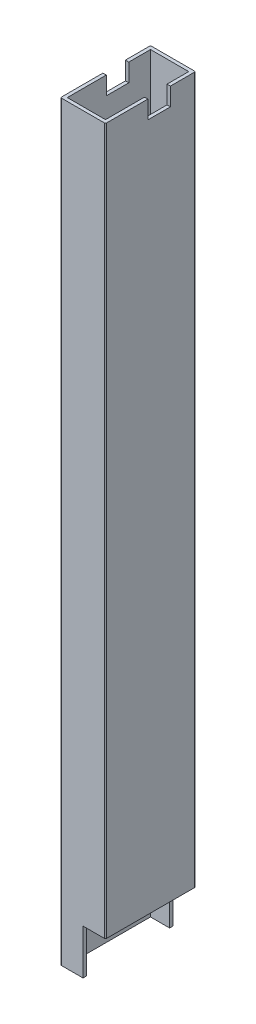
SolidWorks part; units mm, degrees
ref_plane "Front Plane" through (0, 0, 0) normal (0, 0, 1) x (1, 0, 0)
ref_plane "Top Plane" through (0, 0, 0) normal (0, 1, 0) x (1, 0, 0)
ref_plane "Right Plane" through (0, 0, 0) normal (1, 0, 0) x (0, 0, -1)
sketch "Sketch1" plane through (0, 0, 0) normal (0, 1, 0) x (1, 0, 0)
  line L0 (1.5, 1.5) -> (18.5, 1.5)
  line L1 (0.5, 0) -> (19.5, 0)
  line L2 (0, 0.5) -> (0, 39.5)
  line L3 (0.5, 40) -> (19.5, 40)
  line L4 (20, 0.5) -> (20, 39.5)
  line L5 (18.5, 1.5) -> (18.5, 38.5)
  line L6 (1.5, 38.5) -> (18.5, 38.5)
  line L7 (1.5, 1.5) -> (1.5, 38.5)
  arc A0 (19.5, 0) -> (20, 0.5) centre (19.5, 0.5) ccw
  arc A1 (0.5, 0) -> (0, 0.5) centre (0.5, 0.5) cw
  arc A2 (0, 39.5) -> (0.5, 40) centre (0.5, 39.5) cw
  arc A3 (19.5, 40) -> (20, 39.5) centre (19.5, 39.5) cw
  arc A4 (18.5, 1.5) -> (18.5, 1.5) centre (18.5, 1.5) ccw
  arc A5 (18.5, 38.5) -> (18.5, 38.5) centre (18.5, 38.5) cw
  arc A6 (1.5, 38.5) -> (1.5, 38.5) centre (1.5, 38.5) cw
  arc A7 (1.5, 1.5) -> (1.5, 1.5) centre (1.5, 1.5) cw
  point P9 (0, 0)
  dimension "D3" = 0.5
  dimension "D1" = 20
  dimension "D2" = 40
  dimension "D4" = 1.5
extrude "Boss-Extrude1" add sketch "Sketch1" along normal blind 334
sketch "Sketch2" plane through (0, 0, 0) normal (0, 0, 1) x (1, 0, 0)
  line L0 (10, 20) -> (10, 0)
  line L1 (20, 0) -> (10, 0)
  line L2 (20, 0) -> (20, 20)
  line L3 (20, 20) -> (10, 20)
  line L5 (0.5, 0) -> (19.5, 0) construction
  dimension "D1" = 20
extrude "Cut-Extrude1" cut sketch "Sketch2" against normal blind 40
sketch "Sketch3" plane through (0, 0, 0) normal (1, 0, 0) x (0, 0, -1)
  line L6 (0, 334) -> (0, 324)
  line L7 (0, 334) -> (0, 0) construction
  line L8 (0, 324) -> (19.8205, 324)
  line L9 (19.8205, 324) -> (2.5, 334)
  line L10 (39.5, 334) -> (0.5, 334) construction
  line L11 (2.5, 334) -> (0, 334)
  line L12 (17.5, 334) -> (34.8205, 324)
  line L13 (34.8205, 324) -> (40, 324)
  line L14 (40, 334) -> (40, 0) construction
  line L15 (40, 324) -> (40, 334)
  line L16 (40, 334) -> (17.5, 334)
  dimension "D1" = 15
  dimension "D2" = 10
  dimension "D3" = 30
  dimension "10" = 2.5
extrude "Cut-Extrude2" [suppressed] cut sketch "Sketch3" along normal blind 40
sketch "Sketch4" plane through (20, 0, 0) normal (1, 0, 0) x (0, 0, -1)
  line L0 (28.84, 334) -> (28.84, 326)
  line L2 (28.84, 326) -> (18.84, 326)
  line L3 (18.84, 326) -> (18.84, 334)
  line L5 (40, 334) -> (40, 20) construction
  line L11 (28.84, 334) -> (18.84, 334)
  line L13 (0.5, 334) -> (39.5, 334) construction
  dimension "D1" = 11.16
  dimension "D2" = 10
  dimension "D3" = 8
extrude "Cut-Extrude3" cut sketch "Sketch4" against normal through all
